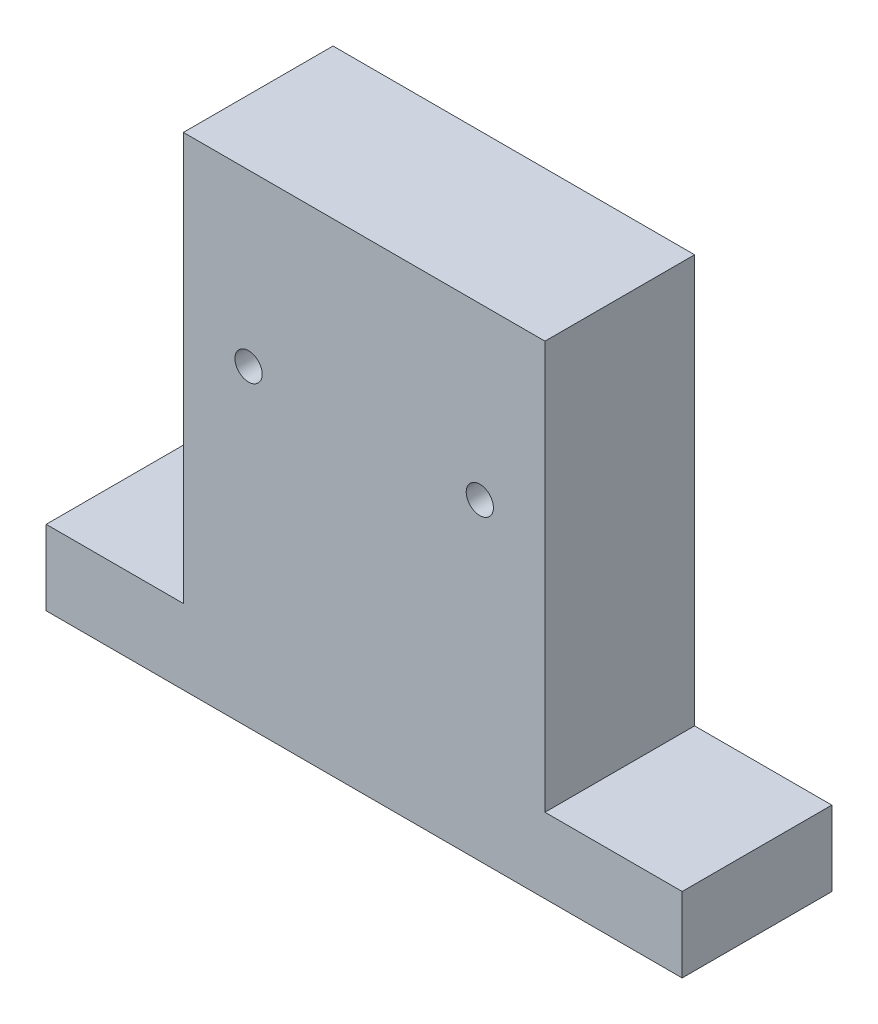
SolidWorks part; units mm, degrees
ref_plane "Front Plane" through (0, 0, 0) normal (0, 0, 1) x (1, 0, 0)
ref_plane "Top Plane" through (0, 0, 0) normal (0, 1, 0) x (1, 0, 0)
ref_plane "Right Plane" through (0, 0, 0) normal (1, 0, 0) x (0, 0, -1)
sketch "Sketch1" plane through (0, 0, 0) normal (0, 0, 1) x (1, 0, 0)
  line L0 (-99.9839, -68.4373) -> (87.0161, -68.4373)
  line L1 (-59.6415, 73.5627) -> (46.6737, 73.5627)
  line L2 (87.0161, -46.4043) -> (87.0161, -68.4373)
  line L3 (-59.6415, -68.4373) -> (-6.4839, -68.4373)
  line L5 (-59.6415, -46.4043) -> (-99.9839, -46.4043)
  line L6 (46.6737, -46.4043) -> (87.0161, -46.4043)
  line L7 (-59.6415, -68.4373) -> (-99.9839, -68.4373)
  line L8 (-99.9839, -46.4043) -> (-99.9839, -68.4373)
  line L11 (-59.6415, -46.4043) -> (-59.6415, 73.5627)
  line L12 (46.6737, -46.4043) -> (46.6737, 73.5627)
  circle A0 centre (-40.4839, 23.5627) radius 4
  circle A1 centre (27.5161, 23.5627) radius 4
  dimension "D1" = 93.5
  dimension "D3" = 142
extrude "Boss-Extrude1" add sketch "Sketch1" along normal blind 44 contours L6 L12 L1 L11 L5 L8 L0 L2 A0 A1
